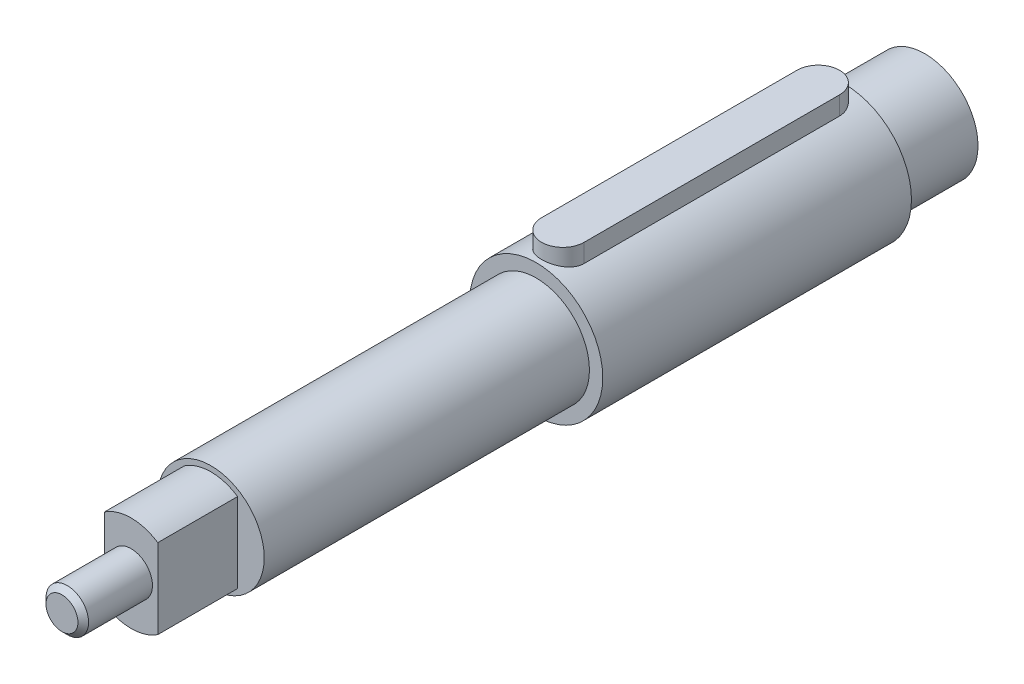
SolidWorks part; units mm, degrees
ref_plane "Alzado" through (0, 0, 0) normal (0, 0, 1) x (1, 0, 0)
ref_plane "Planta" through (0, 0, 0) normal (0, 1, 0) x (1, 0, 0)
ref_plane "Vista lateral" through (0, 0, 0) normal (1, 0, 0) x (0, 0, -1)
sketch "Croquis1" plane through (0, 0, 0) normal (0, 0, 1) x (1, 0, 0)
  circle A0 centre (0, 0) radius 12.5
  dimension "D1" = 25
extrude "Saliente-Extruir1" add sketch "Croquis1" along normal blind 58
sketch "Croquis2" plane through (0, 0, 0) normal (0, 1, 0) x (1, 0, 0)
  line L0 (0, 0) -> (0, -58) construction
  line L1 (-12.5, -58) -> (12.5, -58) construction
  line L2 (0, -5) -> (0, -53) construction
  line L3 (4, -5) -> (4, -53)
  line L4 (-4, -5) -> (-4, -53)
  arc A0 (4, -5) -> (-4, -5) centre (0, -5) ccw
  arc A1 (-4, -53) -> (4, -53) centre (0, -53) ccw
  point P7 (0, -29)
  dimension "D3" = 5
  dimension "D1" = 8
  dimension "D2" = 48
extrude "Cortar-Extruir1" cut sketch "Croquis2" along normal blind 60 from offset 9.3
sketch "Croquis3" plane through (0, 0, 0) normal (0, 0, -1) x (-1, 0, 0)
  circle A0 centre (0, 0) radius 10
  dimension "D1" = 20
extrude "Saliente-Extruir2" add sketch "Croquis3" along normal blind 15
sketch "Croquis4" plane through (0, 0, 58) normal (0, 0, 1) x (1, 0, 0)
  circle A0 centre (0, 0) radius 10
  dimension "D1" = 20
extrude "Saliente-Extruir3" add sketch "Croquis4" along normal blind 61.1
sketch "Croquis5" plane through (0, 0, 119.1) normal (0, 0, 1) x (1, 0, 0)
  line L0 (0, 9) -> (0, -9) construction
  line L1 (-5, 7.4833) -> (-5, -7.4833)
  line L2 (5, 7.4833) -> (5, -7.4833)
  arc A0 (-5, -7.4833) -> (5, -7.4833) centre (0, 0) ccw
  arc A1 (5, 7.4833) -> (-5, 7.4833) centre (0, 0) ccw
  dimension "D1" = 18
  dimension "D2" = 10
extrude "Saliente-Extruir4" add sketch "Croquis5" along normal blind 15
sketch "Croquis6" plane through (0, 0, 134.1) normal (0, 0, 1) x (1, 0, 0)
  circle A0 centre (0, 0) radius 4
  dimension "D1" = 8
extrude "Saliente-Extruir5" add sketch "Croquis6" along normal blind 13
chamfer "Chaflán1" distance 1 angle 45 1 edges at (4, 0, 147.1)
sketch "Croquis7" plane through (0, 9.3, 0) normal (0, 1, 0) x (1, 0, 0)
  line L2 (-4, -5) -> (-4, -53)
  line L3 (4, -53) -> (4, -5)
  line L4 (-4, -5) -> (-4, -53)
  line L5 (4, -53) -> (4, -5)
  arc A2 (4, -5) -> (-4, -5) centre (0, -5) ccw
  arc A3 (-4, -53) -> (4, -53) centre (0, -53) ccw
  arc A4 (4, -5) -> (-4, -5) centre (0, -5) ccw
  arc A5 (-4, -53) -> (4, -53) centre (0, -53) ccw
  dimension "D1" = 0
extrude "Saliente-Extruir6" add sketch "Croquis7" along normal blind 6 separate body
